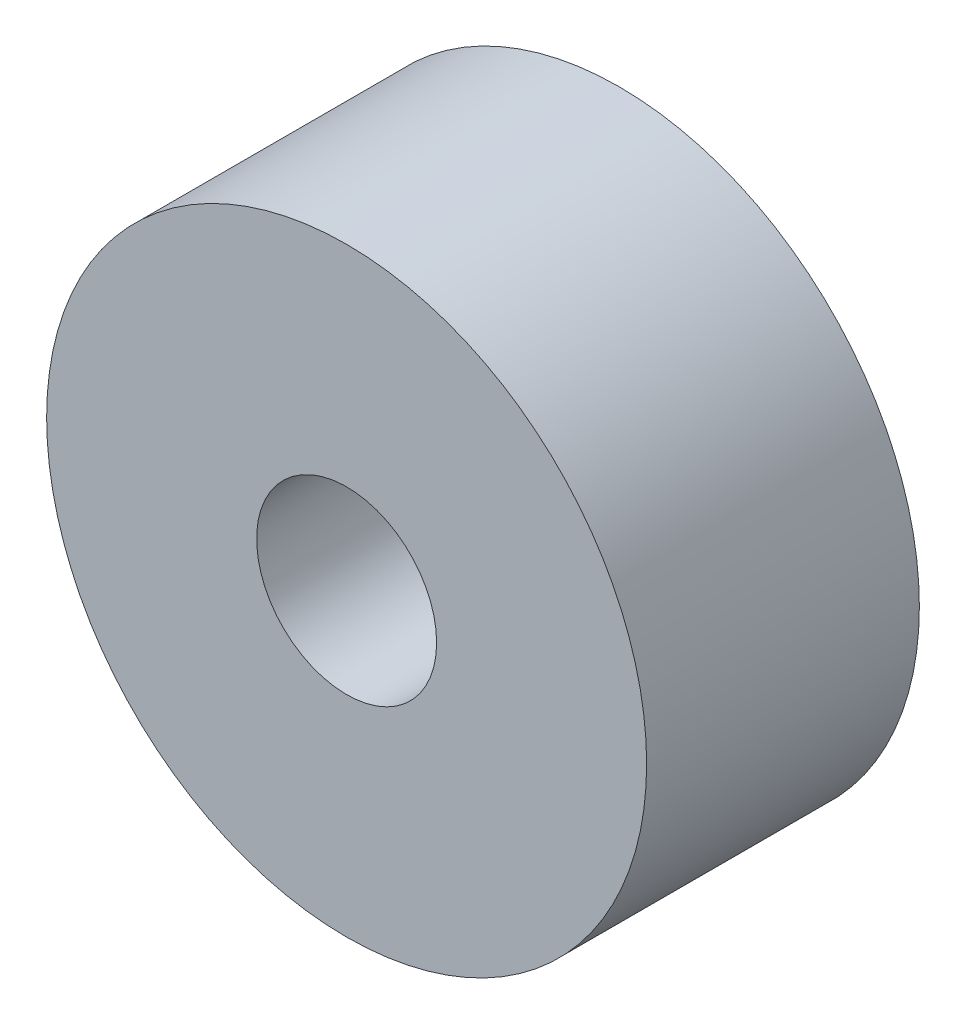
SolidWorks part; units mm, degrees
material "PLA"
ref_plane "Front Plane" through (0, 0, 0) normal (0, 0, 1) x (1, 0, 0)
ref_plane "Top Plane" through (0, 0, 0) normal (0, 1, 0) x (1, 0, 0)
ref_plane "Right Plane" through (0, 0, 0) normal (1, 0, 0) x (0, 0, -1)
sketch "Sketch2" plane through (0, 0, 0) normal (0, 1, 0) x (1, 0, 0)
  line L0 (0, -2.5) -> (0, 2.5) construction
  line L1 (0, 2.5) -> (2.5, 2.5) construction
  line L2 (2.5, 2.5) -> (5.5, 2.5)
  line L3 (0, -2.5) -> (1.65, -2.5) construction
  line L4 (5.5, 2.5) -> (5.5, -2.5)
  line L5 (5.5, -2.5) -> (1.65, -2.5)
  line L6 (1.65, -2.5) -> (1.65, 0)
  line L7 (1.65, 0) -> (2.5, 0)
  line L8 (2.5, 0) -> (2.5, 2.5)
  point P6 (0, 0)
  dimension "D1" = 2.5
  dimension "D2" = 5
  dimension "D3" = 3
  dimension "D4" = 1.65
  dimension "D6" = 2.5
revolve "Revolve1" add sketch "Sketch2" angle 360 about L0
